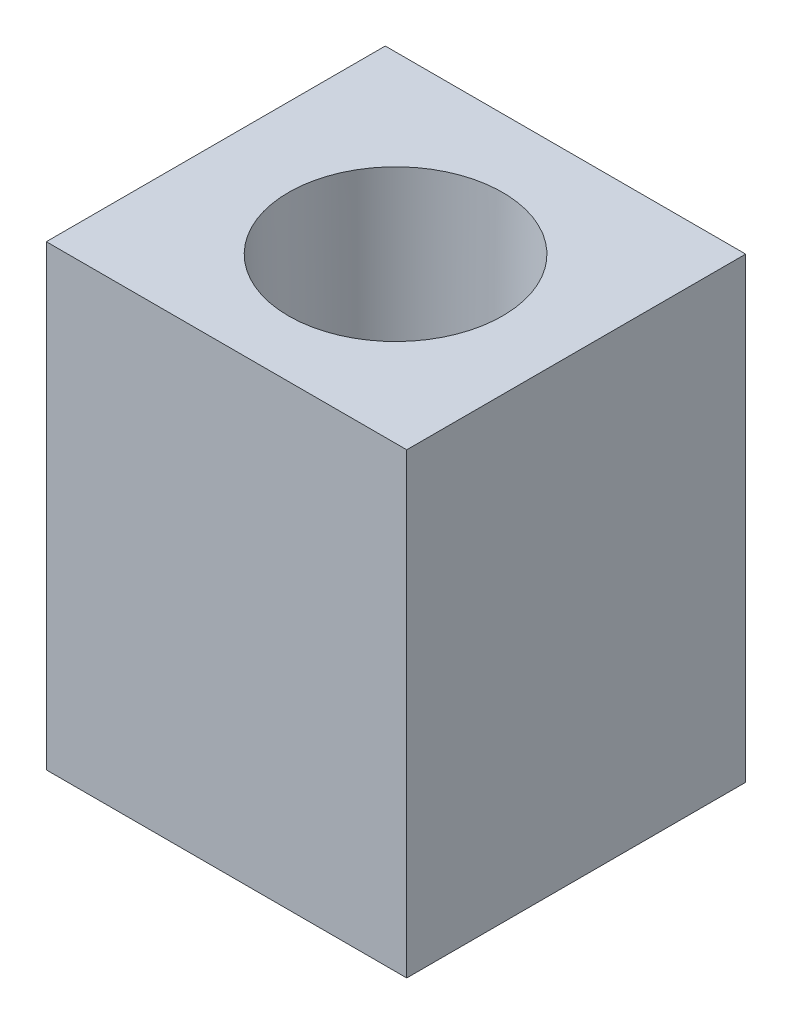
SolidWorks part; units mm, degrees
other "Markup1"
sketch "Sketch12" plane through (4.8578, 0, 4.5481) normal (0.0172, -0.5909, 0.8066) x (0.9998, 0.0028, -0.0192)
ref_plane "Front Plane" through (0, 0, 0) normal (0, 0, 1) x (1, 0, 0)
ref_plane "Top Plane" through (0, 0, 0) normal (0, 1, 0) x (1, 0, 0)
ref_plane "Right Plane" through (0, 0, 0) normal (1, 0, 0) x (0, 0, -1)
sketch "Sketch7" plane through (0, 0, 0) normal (0, 1, 0) x (1, 0, 0)
  line L1 (-5.148, 4.8617) -> (4.8578, 4.8617)
  line L2 (-5.148, 4.8617) -> (-5.148, -4.5481)
  line L3 (-5.148, -4.5481) -> (4.8578, -4.5481)
  line L4 (4.8578, 4.8617) -> (4.8578, -4.5481)
extrude "Boss-Extrude2" add sketch "Sketch7" along normal blind 12.7
sketch "Sketch8" plane through (0, 12.7, 0) normal (0, 1, 0) x (1, 0, 0)
  circle A0 centre (0, 0) radius 2.9718
extrude "Cut-Extrude1" cut sketch "Sketch8" against normal blind 5.588 draft 1.05
sketch "Sketch11" plane through (0, 7.112, 0) normal (0, 1, 0) x (1, 0, 0)
  circle A0 centre (0, 0) radius 2.8694
extrude "Cut-Extrude2" cut sketch "Sketch11" against normal through all
